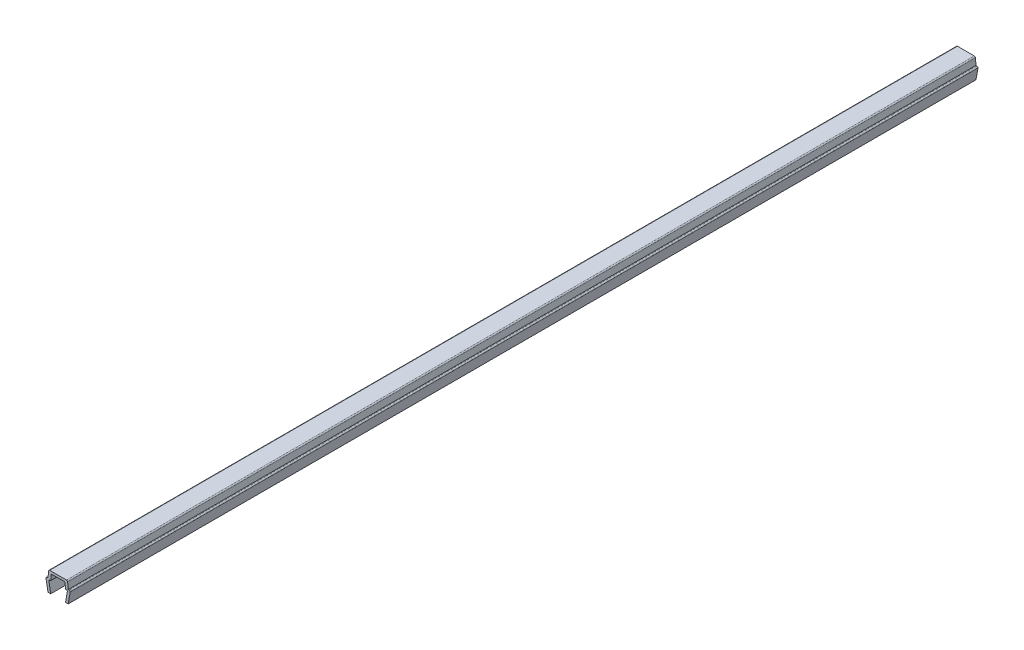
SolidWorks part; units mm, degrees
ref_plane "Front Plane" through (0, 0, 0) normal (0, 0, 1) x (1, 0, 0)
ref_plane "Top Plane" through (0, 0, 0) normal (0, 1, 0) x (1, 0, 0)
ref_plane "Right Plane" through (0, 0, 0) normal (1, 0, 0) x (0, 0, -1)
ref_plane "Plane1" through (0, 0, 0) normal (0, 0, 1) x (1, 0, 0)
sketch "Sketch1" plane through (0, 0, 0) normal (0, 0, 1) x (1, 0, 0)
  line L0 (-3.6, 3.35) -> (-3, 0)
  line L1 (-3, 0) -> (-2.2, 0)
  line L2 (-2.2, 0) -> (-2.7352, 2.9883)
  line L3 (-2.3907, 3.4) -> (-2.2, 3.4)
  line L4 (-2.2, 3.4) -> (-2.0705, 4.8805)
  line L5 (-1.7218, 5.2) -> (1.7218, 5.2)
  line L6 (2.0705, 4.8805) -> (2.2, 3.4)
  line L7 (2.2, 3.4) -> (2.3907, 3.4)
  line L8 (2.7352, 2.9883) -> (2.2, 0)
  line L9 (2.2, 0) -> (3, 0)
  line L10 (3, 0) -> (3.6, 3.35)
  line L11 (3.25, 3.7) -> (3, 3.7)
  line L12 (3, 3.7) -> (2.8355, 5.5805)
  line L13 (2.4868, 5.9) -> (-2.4868, 5.9)
  line L14 (-2.8355, 5.5805) -> (-3, 3.7)
  line L15 (-3, 3.7) -> (-3.25, 3.7)
  arc A0 (-2.7352, 2.9883) -> (-2.3907, 3.4) centre (-2.3907, 3.05) cw
  arc A1 (-2.0705, 4.8805) -> (-1.7218, 5.2) centre (-1.7218, 4.85) cw
  arc A2 (1.7218, 5.2) -> (2.0705, 4.8805) centre (1.7218, 4.85) cw
  arc A3 (2.3907, 3.4) -> (2.7352, 2.9883) centre (2.3907, 3.05) cw
  arc A4 (3.6, 3.35) -> (3.25, 3.7) centre (3.25, 3.35) ccw
  arc A5 (2.8355, 5.5805) -> (2.4868, 5.9) centre (2.4868, 5.55) ccw
  arc A6 (-2.4868, 5.9) -> (-2.8355, 5.5805) centre (-2.4868, 5.55) ccw
  arc A7 (-3.25, 3.7) -> (-3.6, 3.35) centre (-3.25, 3.35) ccw
extrude "Boss-Extrude1" add sketch "Sketch1" against normal mid plane 270
